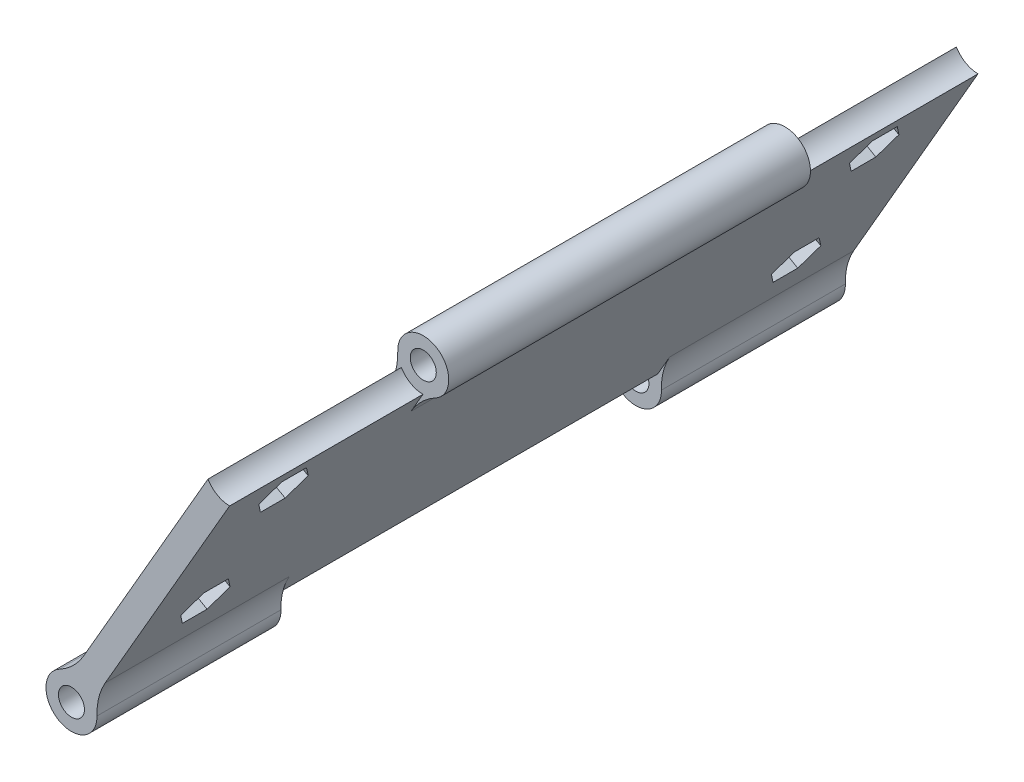
SolidWorks part; units mm, degrees
ref_plane "Front Plane" through (0, 0, 0) normal (0, 0, 1) x (1, 0, 0)
ref_plane "Top Plane" through (0, 0, 0) normal (0, 1, 0) x (1, 0, 0)
ref_plane "Right Plane" through (0, 0, 0) normal (1, 0, 0) x (0, 0, -1)
sketch "Sketch2" plane through (0, 0, 0) normal (0, 0, 1) x (1, 0, 0)
  line L0 (0, 0) -> (38.1, 0)
  line L1 (0, 0) -> (0, -38.1)
  circle A0 centre (0, 0) radius 38.1
  circle A1 centre (0, -29.337) radius 1.5875
  circle A2 centre (-25.4066, 14.6685) radius 1.5875
  circle A3 centre (25.4066, 14.6685) radius 1.5875
  point P13 (0, 0)
  dimension "D1" = 76.2
  dimension "D2" = 3.175
  dimension "D3" = 8.763
  dimension "D4" = 3
extrude "Boss-Extrude1" add sketch "Sketch2" along normal blind 10 contours A1 L1 L0 A0 A3 A2 | A1 L1 A0 L0
sketch "Sketch3" plane through (0, 0, 10) normal (0, 0, 1) x (1, 0, 0)
  line L1 (0, -29.337) -> (25.4066, 14.6685)
  line L2 (1.7321, -30.337) -> (27.1386, 13.6685)
  line L3 (-1.7321, -28.337) -> (23.6745, 15.6685)
  circle A11 centre (0, -29.337) radius 1.5875
  circle A12 centre (25.4066, 14.6685) radius 1.5875
  circle A17 centre (0, -29.337) radius 2.0875
  circle A18 centre (25.4066, 14.6685) radius 2.0875
  circle A19 centre (0, -29.337) radius 4.0875
  circle A20 centre (25.4066, 14.6685) radius 4.0875
  dimension "D1" = 0.5
  dimension "D2" = 2
  dimension "D4" = 2
  dimension "D5" = 2
extrude "Boss-Extrude2" add sketch "Sketch3" along normal blind 120 separate body contours L2 A20 L3 A18 | L1 A20 L2 A18 | L3 A20 L1 A18 | A20 L1 A19 L2 | A20 L3 A19 L1 | L1 A19 L3 A17 | L2 A19 L1 A17 | L3 A19 L2 A17
delete or keep bodies "Body-Delete/Keep 2" type delete bodies bodies 101
ref_plane "Plane1" through (0, 0, 70) normal (0, 0, 1) x (1, 0, 0)
sketch "Sketch4" plane through (0, 0, 70) normal (0, 0, 1) x (1, 0, 0)
  circle A1 centre (0, -29.337) radius 4.0875
extrude "Cut-Extrude1" cut sketch "Sketch4" against normal blind 30.5 and the other way blind 30.5
sketch "Sketch5" plane through (0, 0, 10) normal (0, 0, -1) x (-1, 0, 0)
  circle A0 centre (-25.4066, 14.6685) radius 4.0875
extrude "Cut-Extrude2" cut sketch "Sketch5" against normal offset from surface (31 mm away) 1.5 up to face at (2.0875, -29.337, 39.5) offset beyond the face yes
sketch "Sketch6" plane through (0, 0, 130) normal (0, 0, 1) x (1, 0, 0)
  circle A0 centre (25.4066, 14.6685) radius 4.0875
extrude "Cut-Extrude3" cut sketch "Sketch6" against normal offset from surface (31 mm away) 1.5 contours A0 up to face at (2.0875, -29.337, 100.5) offset beyond the face yes
fillet "Fillet1" radius 10 6 edges at (21.8921, 12.5813, 70) (0.0503, -25.2498, 24.75) (0.0503, -25.2498, 115.25) (3.5144, -27.2498, 115.25) (3.5144, -27.2498, 24.75) (25.3562, 10.5813, 70)
sketch "Sketch7" plane through (10.9712, -6.3342, 0) normal (-0.866, 0.5, 0) x (0, 0, 1)
  circle A0 centre (23.772, -8.9489) radius 1.75
  circle A1 centre (23.772, 16.0955) radius 1.75
  circle A2 centre (118.4886, 16.0955) radius 1.75
  circle A3 centre (118.4886, -8.9489) radius 1.75
  dimension "D1" = 3.5
extrude "Cut-Extrude4" cut sketch "Sketch7" against normal up to surface (4 mm away) up to face at (14.7532, -7.7836, 70)
sketch "Sketch8" plane through (14.4353, -8.3342, 0) normal (0.866, -0.5, 0) x (0, 0, -1)
  line L1 (-19.8125, 16.0955) -> (-21.7922, 19.5245)
  line L2 (-21.7922, 19.5245) -> (-25.7517, 19.5245)
  line L3 (-25.7517, 19.5245) -> (-27.7314, 16.0955)
  line L4 (-27.7314, 16.0955) -> (-25.7517, 12.6665)
  line L5 (-25.7517, 12.6665) -> (-21.7922, 12.6665)
  line L6 (-21.7922, 12.6665) -> (-19.8125, 16.0955)
  line L7 (-19.8125, -8.9489) -> (-21.7922, -5.5199)
  line L8 (-21.7922, -5.5199) -> (-25.7517, -5.5199)
  line L9 (-25.7517, -5.5199) -> (-27.7314, -8.9489)
  line L10 (-27.7314, -8.9489) -> (-25.7517, -12.3779)
  line L11 (-25.7517, -12.3779) -> (-21.7922, -12.3779)
  line L12 (-21.7922, -12.3779) -> (-19.8125, -8.9489)
  line L13 (-114.5291, 16.0955) -> (-116.5088, 19.5245)
  line L14 (-116.5088, 19.5245) -> (-120.4683, 19.5245)
  line L15 (-120.4683, 19.5245) -> (-122.448, 16.0955)
  line L16 (-122.448, 16.0955) -> (-120.4683, 12.6665)
  line L17 (-120.4683, 12.6665) -> (-116.5088, 12.6665)
  line L18 (-116.5088, 12.6665) -> (-114.5291, 16.0955)
  line L25 (-114.5291, -8.9489) -> (-116.5088, -5.5199)
  line L26 (-116.5088, -5.5199) -> (-120.4683, -5.5199)
  line L27 (-120.4683, -5.5199) -> (-122.448, -8.9489)
  line L28 (-122.448, -8.9489) -> (-120.4683, -12.3779)
  line L29 (-120.4683, -12.3779) -> (-116.5088, -12.3779)
  line L30 (-116.5088, -12.3779) -> (-114.5291, -8.9489)
  circle A0 centre (-23.772, 16.0955) radius 3.429 construction
  circle A1 centre (-23.772, -8.9489) radius 3.429 construction
  circle A2 centre (-118.4886, 16.0955) radius 3.429 construction
  circle A3 centre (-118.4886, -8.9489) radius 3.429 construction
  dimension "D1" = 6.858
extrude "Cut-Extrude5" cut sketch "Sketch8" against normal blind 2.25
